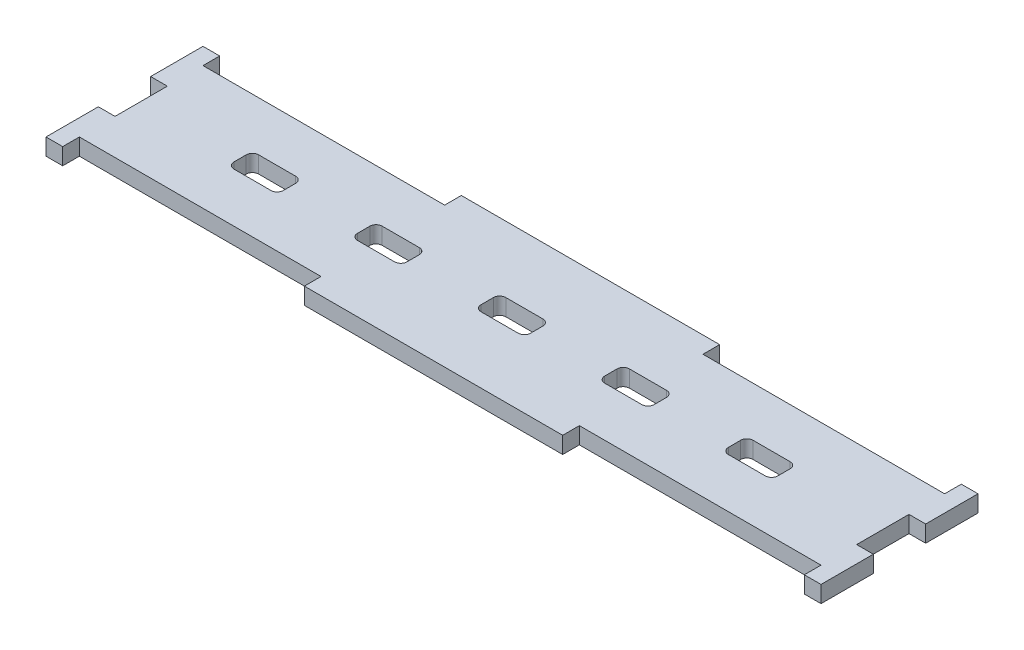
SolidWorks part; units mm, degrees
ref_plane "Front Plane" through (0, 0, 0) normal (0, 0, 1) x (1, 0, 0)
ref_plane "Top Plane" through (0, 0, 0) normal (0, 1, 0) x (1, 0, 0)
ref_plane "Right Plane" through (0, 0, 0) normal (1, 0, 0) x (0, 0, -1)
sketch "Sketch1" plane through (0, 0, 0) normal (0, 1, 0) x (1, 0, 0)
  line L0 (-62.7, 12.7) -> (-60, 12.7)
  line L1 (-60, 10) -> (-20.9, 10)
  line L2 (-60, 4.2333) -> (-60, -4.2333)
  line L3 (-60, -10) -> (-20.9, -10)
  line L4 (60, 4.2333) -> (60, -4.2333)
  line L5 (-60, 10) -> (60, -10) construction
  line L6 (-60, -10) -> (60, 10) construction
  line L7 (62.7, 12.7) -> (62.7, 4.2333)
  line L8 (-62.7, -12.7) -> (-60, -12.7)
  line L9 (-62.7, 12.7) -> (-62.7, 4.2333)
  line L10 (-60, 10) -> (-60, 12.7)
  line L11 (-60, -10) -> (-60, -12.7)
  line L12 (60, 10) -> (60, 12.7)
  line L13 (60, -10) -> (60, -12.7)
  line L14 (-20.9, 12.7) -> (20.9, 12.7)
  line L15 (-62.7, 12.7) -> (62.7, 12.7) construction
  line L16 (60, 12.7) -> (62.7, 12.7)
  line L17 (-20.9, -12.7) -> (20.9, -12.7)
  line L18 (-62.7, -12.7) -> (62.7, -12.7) construction
  line L19 (60, -12.7) -> (62.7, -12.7)
  line L20 (-20.9, 12.7) -> (-20.9, 10)
  line L21 (20.9, 12.7) -> (20.9, 10)
  line L22 (20.9, -12.7) -> (20.9, -10)
  line L23 (-20.9, -12.7) -> (-20.9, -10)
  line L25 (-62.7, 12.7) -> (-62.7, -12.7) construction
  line L26 (-62.7, -4.2333) -> (-62.7, -12.7)
  line L28 (62.7, 12.7) -> (62.7, -12.7) construction
  line L29 (62.7, -4.2333) -> (62.7, -12.7)
  line L30 (-62.7, 4.2333) -> (-60, 4.2333)
  line L31 (-62.7, -4.2333) -> (-60, -4.2333)
  line L32 (62.7, 4.2333) -> (60, 4.2333)
  line L33 (62.7, -4.2333) -> (60, -4.2333)
  line L34 (20.9, 10) -> (60, 10)
  line L35 (-60, 10) -> (60, 10) construction
  line L36 (60, 10) -> (60, -10) construction
  line L37 (20.9, -10) -> (60, -10)
  line L38 (-60, -10) -> (60, -10) construction
  line L39 (-60, 10) -> (-60, -10) construction
  line L42 (-37, 2) -> (-43, 2)
  line L43 (-36, 1) -> (-36, -1)
  line L44 (-37, -2) -> (-43, -2)
  line L45 (-44, 1) -> (-44, -1)
  line L46 (-36, 2) -> (-44, -2) construction
  line L47 (-36, -2) -> (-44, 2) construction
  line L48 (-23, 2) -> (-17, 2)
  line L49 (-24, 1) -> (-24, -1)
  line L50 (-23, -2) -> (-17, -2)
  line L51 (-16, 1) -> (-16, -1)
  line L52 (-24, 2) -> (-16, -2) construction
  line L53 (-24, -2) -> (-16, 2) construction
  line L54 (-3, 2) -> (3, 2)
  line L55 (-4, 1) -> (-4, -1)
  line L56 (-3, -2) -> (3, -2)
  line L57 (4, 1) -> (4, -1)
  line L58 (-4, 2) -> (4, -2) construction
  line L59 (-4, -2) -> (4, 2) construction
  line L60 (17, 2) -> (23, 2)
  line L61 (16, 1) -> (16, -1)
  line L62 (17, -2) -> (23, -2)
  line L63 (24, 1) -> (24, -1)
  line L64 (16, 2) -> (24, -2) construction
  line L65 (16, -2) -> (24, 2) construction
  line L66 (37, 2) -> (43, 2)
  line L67 (36, 1) -> (36, -1)
  line L68 (37, -2) -> (43, -2)
  line L69 (44, 1) -> (44, -1)
  line L70 (36, 2) -> (44, -2) construction
  line L71 (36, -2) -> (44, 2) construction
  arc A0 (-37, 2) -> (-36, 1) centre (-37, 1) cw
  arc A1 (-36, -1) -> (-37, -2) centre (-37, -1) cw
  arc A2 (-43, -2) -> (-44, -1) centre (-43, -1) cw
  arc A3 (-44, 1) -> (-43, 2) centre (-43, 1) cw
  arc A4 (-24, -1) -> (-23, -2) centre (-23, -1) ccw
  arc A5 (-17, -2) -> (-16, -1) centre (-17, -1) ccw
  arc A6 (-16, 1) -> (-17, 2) centre (-17, 1) ccw
  arc A7 (-23, 2) -> (-24, 1) centre (-23, 1) ccw
  arc A8 (-4, -1) -> (-3, -2) centre (-3, -1) ccw
  arc A9 (3, -2) -> (4, -1) centre (3, -1) ccw
  arc A10 (4, 1) -> (3, 2) centre (3, 1) ccw
  arc A11 (-3, 2) -> (-4, 1) centre (-3, 1) ccw
  arc A12 (16, -1) -> (17, -2) centre (17, -1) ccw
  arc A13 (23, -2) -> (24, -1) centre (23, -1) ccw
  arc A14 (24, 1) -> (23, 2) centre (23, 1) ccw
  arc A15 (17, 2) -> (16, 1) centre (17, 1) ccw
  arc A16 (36, -1) -> (37, -2) centre (37, -1) ccw
  arc A17 (43, -2) -> (44, -1) centre (43, -1) ccw
  arc A18 (44, 1) -> (43, 2) centre (43, 1) ccw
  arc A19 (37, 2) -> (36, 1) centre (37, 1) ccw
  point P0 (0, 0)
  point P32 (-40, 0)
  point P33 (-20, 0)
  point P34 (0, 0)
  point P35 (20, 0)
  point P36 (40, 0)
  point P37 (-40, 0)
  point P54 (-20, 0)
  point P59 (0, 0)
  point P64 (20, 0)
  point P69 (40, 0)
  dimension "D6" = 1
  dimension "D15" = 1
  dimension "D16" = 1
  dimension "D17" = 1
  dimension "D18" = 1
  dimension "D1" = 20
  dimension "D2" = 120
  dimension "D4" = 8
  dimension "D5" = 4
  dimension "D7" = 8
  dimension "D8" = 8
  dimension "D9" = 8
  dimension "D10" = 8
  dimension "D11" = 4
  dimension "D12" = 4
  dimension "D13" = 4
  dimension "D14" = 4
  dimension "D3" = 2.7
extrude "Boss-Extrude1" add sketch "Sketch1" along normal blind 2.7
